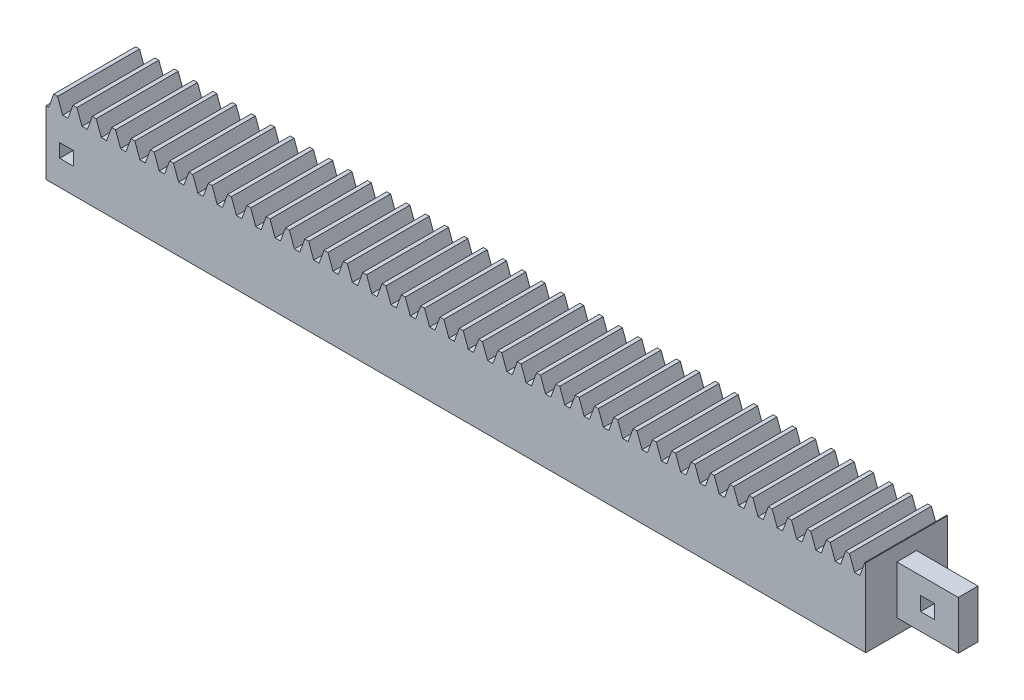
SolidWorks part; units mm, degrees
extrude "Blank" add sketch "BlankSke" against normal blind 20
sketch "BlankSke" plane through (0, 0, 0) normal (0, 0, 1) x (1, 0, 0)
  line L1 (0, 0) -> (200, 0)
  line L2 (0, 0) -> (0, 19)
  line L3 (0, 19) -> (200, 19)
  line L4 (200, 0) -> (200, 19)
  dimension "Length" = 200
  dimension "Blank_height" = 19
ref_plane "Plane1" through (0, 0, 0) normal (0, 0, 1) x (1, 0, 0)
ref_plane "Plane2" through (0, 0, 0) normal (0, 1, 0) x (1, 0, 0)
ref_plane "Plane3" through (0, 0, 0) normal (1, 0, 0) x (0, 0, -1)
other "Configuration Table"
sketch "HoldingSke" plane through (0, 0, 0) normal (0, 1, 0) x (1, 0, 0)
  line L0 (0, 0) -> (0.0928, 0.6602)
  line L1 (-15, 0) -> (100, 0) construction
  line L2 (0, 0) -> (-2.1039, 2.3779)
  line L3 (0, 0) -> (-11.863, 4.5341)
  line L4 (0, 0) -> (6.2122, 5.9991)
  line L5 (0, 0) -> (-23.7986, -8.8762)
  line L6 (0, 0) -> (-10.5278, -7.1032)
  line L9 (-71.009, 38.7566) -> (116.9296, 107.1606)
  line L10 (-76.2, 3.8779) -> (-58.7, 3.8779)
  line L11 (0, 0) -> (-20, 0)
  line L12 (-76.2, 101.6) -> (-76.147, 101.6)
  line L13 (24.9733, 27.94) -> (52.9518, 28.4284)
  line L14 (24.9733, 27.94) -> (24.9743, 27.94)
  line L15 (24.9733, 27.94) -> (100.4006, 29.5858)
  circle A0 centre (0, 0) radius 19.05
  circle A1 centre (0, 0) radius 8.75
  circle A2 centre (0, 0) radius 12.7
  dimension "MPH" = 17.5
  dimension "Diameter" = 38.1
  dimension "Num_teeth" = 44
  dimension "Pitch" = 0.6667
  dimension "Show_teeth" = 998
  dimension "Thickness" = 12.7
  dimension "Ap" = 20
  dimension "Pitch_height" = 17.5
  dimension "Width" = 20
  dimension "Backlash" = 0.053
  dimension "Addendum_fac" = 1
  dimension "Dedendum_fac" = 1.25
  dimension "Clearance_fac" = 0.25
  dimension "Dedendum_add" = 0.001
  dimension "Length" = 200
  dimension "Module" = 1.5
sketch "TooCutSkeIll" plane through (0, 0, 0) normal (0, 0, 1) x (1, 0, 0)
  line L0 (-1.8687, 18.9605) -> (-0.7447, 15.8724)
  line L1 (-0.3914, 15.625) -> (0.3914, 15.625)
  line L2 (0.7447, 15.8724) -> (1.8687, 18.9605)
  line L3 (200, 19) -> (0, 19) construction
  line L4 (0, 0) -> (0, 64.897) construction
  line L5 (-13.208, 17.5) -> (12.954, 17.5) construction
  line L6 (0, 0) -> (200, 0) construction
  line L7 (1.3371, 17.5) -> (1.3371, 48.7463) construction
  line L8 (-1.3371, 17.5) -> (-1.3371, 48.7463) construction
  line L9 (1.9251, 19) -> (1.9251, 19.0254)
  line L10 (-1.9251, 19) -> (-1.9251, 19.0254)
  line L11 (-1.9251, 19.0254) -> (1.9251, 19.0254)
  arc A0 (0.3914, 15.625) -> (0.7447, 15.8724) centre (0.3914, 16.001) ccw
  arc A1 (-0.7447, 15.8724) -> (-0.3914, 15.625) centre (-0.3914, 16.001) ccw
  arc A2 (1.9251, 19) -> (1.8687, 18.9605) centre (1.9251, 18.94) ccw
  arc A3 (-1.8687, 18.9605) -> (-1.9251, 19) centre (-1.9251, 18.94) ccw
  dimension "Pitch_height" = 17.5
  dimension "Addendum_plus" = 1.5254
  dimension "Pressure_angle" = 20
  dimension "Gap_width" = 2.6742
  dimension "Dedendum" = 1.875
extrude "ToothCutIll" [suppressed] cut sketch "TooCutSkeIll" against normal through all
sketch "TooCutSkeSim" plane through (0, 0, 0) normal (0, 0, 1) x (1, 0, 0)
  line L0 (0.6547, 15.625) -> (-0.6547, 15.625)
  line L1 (1.8923, 19.0254) -> (0.6547, 15.625)
  line L2 (0, 17.4625) -> (0, 53.467) construction
  line L3 (1.8923, 19.0254) -> (-1.8923, 19.0254)
  line L6 (-1.8923, 19.0254) -> (-0.6547, 15.625)
  line L9 (-1.3371, 17.5) -> (1.3371, 17.5) construction
  line L10 (0, 0) -> (200, 0) construction
  line L11 (1.3371, 17.5) -> (1.3371, 53.467) construction
  line L12 (-1.3371, 17.5) -> (-1.3371, 53.467) construction
  dimension "Pitch_height" = 17.5
  dimension "Addendum_plus" = 1.5254
  dimension "Pressure_angle" = 20
  dimension "Gap_width" = 2.6742
  dimension "Dedendum" = 1.875
extrude "ToothCutSim" cut sketch "TooCutSkeSim" against normal through all
pattern_linear "TeethCuts" count 43 spacing 4.7124 along (1, 0, 0) of "ToothCutIll", "ToothCutSim"
sketch "Sketch1" plane through (200, 0, 0) normal (1, 0, 0) x (0, 0, -1)
  line L0 (20, 0) -> (0, 0) construction
  line L1 (7.6, 0) -> (12.4, 0)
  line L2 (7.6, 0) -> (7.6, 19)
  line L3 (7.6, 19) -> (12.4, 19)
  line L4 (12.4, 0) -> (12.4, 19)
  line L5 (20, 19) -> (0, 19) construction
  point P8 (10, 0)
  point P9 (10, 0)
  dimension "D1" = 4.8
extrude "Boss-Extrude1" add sketch "Sketch1" along normal blind 15
sketch "Sketch2" plane through (0, 0, -12.4) normal (0, 0, -1) x (-1, 0, 0)
  line L0 (-200, 0) -> (-200, 19) construction
  line L1 (-215, 19) -> (-200, 19)
  line L2 (-215, 19) -> (-215, 15.4)
  line L3 (-215, 15.4) -> (-200, 15.4)
  line L4 (-200, 19) -> (-200, 15.4)
  line L5 (-200, 0) -> (-200, 19) construction
  line L6 (-215, 0) -> (-200, 0)
  line L7 (-215, 0) -> (-215, 3.6)
  line L8 (-215, 3.6) -> (-200, 3.6)
  line L9 (-200, 0) -> (-200, 3.6)
  line L10 (-215, 3.6) -> (-200, 15.4) construction
  line L11 (-200, 3.6) -> (-215, 15.4) construction
  line L13 (-209.2, 11.2) -> (-205.8, 11.2)
  line L14 (-209.2, 11.2) -> (-209.2, 7.8)
  line L15 (-209.2, 7.8) -> (-205.8, 7.8)
  line L16 (-205.8, 11.2) -> (-205.8, 7.8)
  line L17 (-209.2, 11.2) -> (-205.8, 7.8) construction
  line L18 (-209.2, 7.8) -> (-205.8, 11.2) construction
  point P14 (-207.5, 9.5)
  dimension "D3" = 3.4
  dimension "D1" = 3.6
  dimension "D2" = 3.6
  dimension "D4" = 3.4
extrude "Cut-Extrude1" cut sketch "Sketch2" against normal up to surface (4.8 mm away) up to face at (207.5, 9.5, -7.6)
sketch "Sketch3" plane through (0, 0, 0) normal (-1, 0, 0) x (0, 0, 1)
  line L1 (-13.5, 11.3125) -> (-6.5, 11.3125)
  line L2 (-13.5, 11.3125) -> (-13.5, 4.3125)
  line L3 (-13.5, 4.3125) -> (-6.5, 4.3125)
  line L4 (-6.5, 11.3125) -> (-6.5, 4.3125)
  line L5 (-20, 15.625) -> (0, 0) construction
  line L6 (-20, 0) -> (0, 15.625) construction
  line L7 (-13.5, 11.3125) -> (-6.5, 4.3125) construction
  line L8 (-13.5, 4.3125) -> (-6.5, 11.3125) construction
  point P12 (-10, 7.8125)
  point P14 (-10, 7.8125)
  dimension "D1" = 7
extrude "Cut-Extrude3" cut sketch "Sketch3" against normal blind 10
sketch "Sketch4" plane through (0, 0, -20) normal (0, 0, -1) x (-1, 0, 0)
  line L1 (0, 15.625) -> (0, 0) construction
  line L2 (-6.65, 9.4625) -> (-3.35, 9.4625)
  line L3 (-6.65, 9.4625) -> (-6.65, 6.1625)
  line L4 (-6.65, 6.1625) -> (-3.35, 6.1625)
  line L5 (-3.35, 9.4625) -> (-3.35, 6.1625)
  line L6 (0, 7.8125) -> (-10.1116, 7.8125) construction
  line L7 (-6.65, 9.4625) -> (-3.35, 6.1625) construction
  point P8 (-5, 7.8125)
  dimension "D1" = 3.3
  dimension "D2" = 3.35
extrude "Cut-Extrude4" cut sketch "Sketch4" against normal blind 25
equation "' \"Module@HoldingSke\" = 6.35"
equation "' \"Num_teeth@HoldingSke\" = 12"
equation "' \"Ap@HoldingSke\" =  20"
equation "' \"Ap@HoldingSke\" = 20"
equation "' \"Width@HoldingSke\" = 0.25 * 25.4"
equation "' \"Show_teeth@HoldingSke\" = 500"
equation "' \"Backlash@HoldingSke\" = 0.009 * 25.4"
equation "' \"Addendum_fac@HoldingSke\" = 1.0"
equation "' \"Dedendum_fac@HoldingSke\" = 1.25"
equation "' \"Dedendum_add@HoldingSke\" = 0.00005 * 25.4"
equation "' \"Clearance_fac@HoldingSke\" = 0.25"
equation "' \"Pitch_height@HoldingSke\" = 1 * 25.4"
equation "' \"Length@HoldingSke\" = 4.71 * 25.4"
equation "\"Pitch@HoldingSke\" = 1 / \"Module@HoldingSke\""
equation "\"MPH@HoldingSke\" = \"Dedendum_fac@HoldingSke\" / \"Pitch@HoldingSke\" + 2 * \"Dedendum_add@HoldingSke\" + 0.002 * 25.4"
equation "\"MPH@HoldingSke\" = ((sgn( \"MPH@HoldingSke\" - \"Pitch_height@HoldingSke\")+1)*( \"MPH@HoldingSke\" - \"Pitch_height@HoldingSke\"))/2 + \"Pitch_height@HoldingSke\""
equation "\"Blank_height@BlankSke\" = \"Pitch_height@HoldingSke\" + \"Addendum_fac@HoldingSke\"  / \"Pitch@HoldingSke\" "
equation "\"Length@BlankSke\" =  \"Length@HoldingSke\""
equation "\"Face_width@Blank\" = \"Width@HoldingSke\""
equation "\"Pressure_angle@TooCutSkeIll\" = \"Ap@HoldingSke\""
equation "\"Addendum_plus@TooCutSkeIll\" =  \"Addendum_fac@HoldingSke\"  / \"Pitch@HoldingSke\" + 0.001 *25.4"
equation "\"Dedendum@TooCutSkeIll\" = \"Dedendum_fac@HoldingSke\"  / \"Pitch@HoldingSke\""
equation "\"Pitch_height@TooCutSkeIll\" =  \"MPH@HoldingSke\""
equation "\"Gap_width@TooCutSkeIll\" = 3.14159265 / 2 / \"Pitch@HoldingSke\" + 6 * \"Backlash@HoldingSke\""
equation "\"Pressure_angle@TooCutSkeSim\" = \"Ap@HoldingSke\""
equation "\"Addendum_plus@TooCutSkeSim\" =  \"Addendum_fac@HoldingSke\"  / \"Pitch@HoldingSke\" + 0.001 * 25.4"
equation "\"Dedendum@TooCutSkeSim\" = \"Dedendum_fac@HoldingSke\"  / \"Pitch@HoldingSke\""
equation "\"Pitch_height@TooCutSkeSim\" =  \"MPH@HoldingSke\""
equation "\"Gap_width@TooCutSkeSim\" = 3.14159265 / 2 / \"Pitch@HoldingSke\" + 6 * \"Backlash@HoldingSke\""
equation "\"Root_fillet@TooCutSkeIll\" = \"Clearance_fac@HoldingSke\" / \"Pitch@HoldingSke\" + \"Dedendum_add@HoldingSke\""
equation "\"Break_rad@TooCutSkeIll\" = 0.02 / \"Pitch@HoldingSke\" * 2"
equation "\"Linear_pitch@TeethCuts\" = 3.14159265 / \"Pitch@HoldingSke\""
equation "\"Num_teeth@HoldingSke\" = int( ( \"Length@HoldingSke\" + 0 ) / (3.14159265 / \"Pitch@HoldingSke\")) + 0.9999  + 1"
equation " \"Num_teeth@TeethCuts\" = int( \"Show_teeth@HoldingSke\" ) + 1"
equation " \"Num_teeth@TeethCuts\" = ((sgn( \"Num_teeth@TeethCuts\" - \"Num_teeth@HoldingSke\" )-1)*( \"Num_teeth@TeethCuts\" - \"Num_teeth@HoldingSke\" ))/-2+ \"Num_teeth@HoldingSke\""
equation " \"Num_teeth@TeethCuts\" = ((sgn( \"Num_teeth@TeethCuts\" - 2.0)+1)*( \"Num_teeth@TeethCuts\" - 2.0))/2 +2.0"
